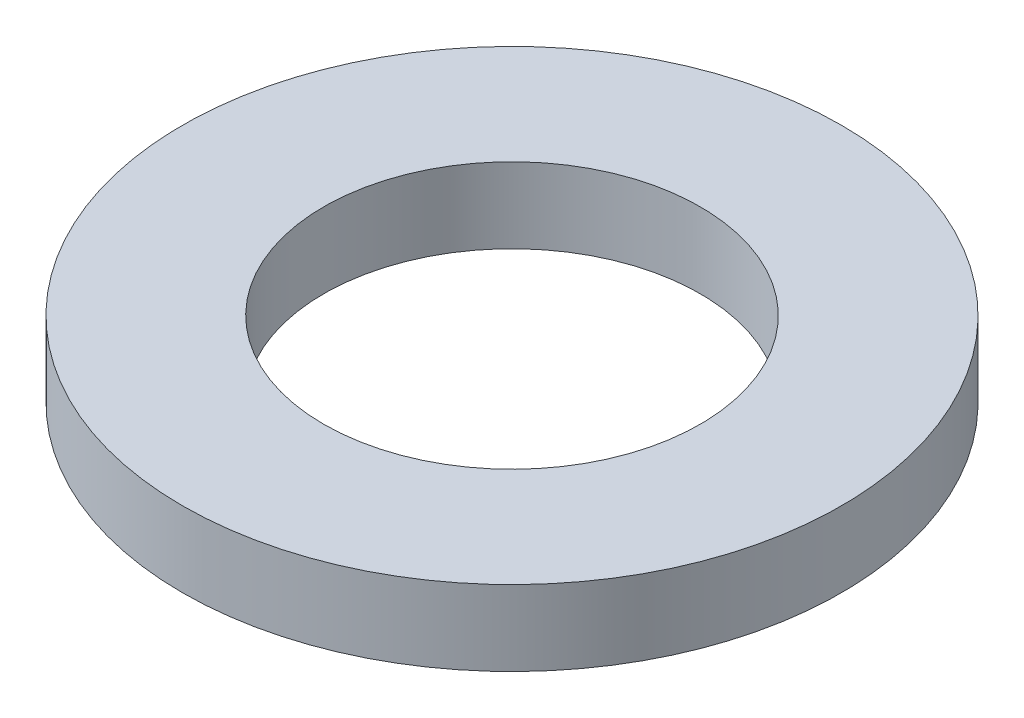
SolidWorks part; units mm, degrees
material "AISI 1020 Steel, Cold Rolled"
ref_plane "Front Plane" through (0, 0, 0) normal (0, 0, 1) x (1, 0, 0)
ref_plane "Top Plane" through (0, 0, 0) normal (0, 1, 0) x (1, 0, 0)
ref_plane "Right Plane" through (0, 0, 0) normal (1, 0, 0) x (0, 0, -1)
sketch "Sketch1" plane through (0, 0, 0) normal (0, 1, 0) x (1, 0, 0)
  circle A0 centre (0, 0) radius 4
  circle A1 centre (0, 0) radius 7
  dimension "D1" = 8
  dimension "D2" = 14
extrude "Boss-Extrude1" add sketch "Sketch1" along normal blind 1.6
